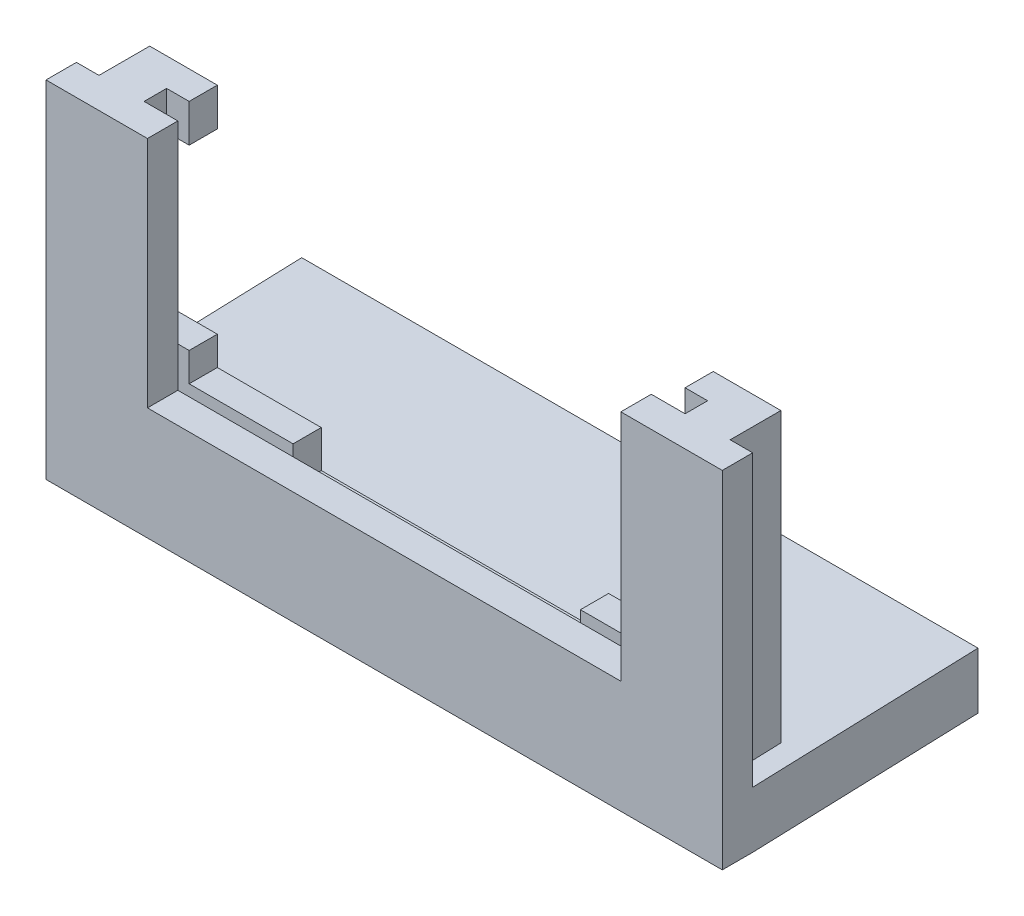
SolidWorks part; units mm, degrees
ref_plane "Front Plane" through (0, 0, 0) normal (0, 0, 1) x (1, 0, 0)
ref_plane "Top Plane" through (0, 0, 0) normal (0, 1, 0) x (1, 0, 0)
ref_plane "Right Plane" through (0, 0, 0) normal (1, 0, 0) x (0, 0, -1)
sketch "Sketch1" plane through (0, 0, 0) normal (0, 0, 1) x (1, 0, 0)
  line L0 (-33.3735, 36.8475) -> (-33.3735, -13.1525) construction
  line L1 (-63.3735, 36.8475) -> (-3.3735, 36.8475)
  line L2 (-63.3735, 36.8475) -> (-63.3735, -23.1525)
  line L3 (-63.3735, -23.1525) -> (-3.3735, -23.1525)
  line L4 (-3.3735, 36.8475) -> (-3.3735, -23.1525)
  line L5 (-54.3735, -13.1525) -> (-12.3735, -13.1525)
  line L6 (-12.3735, -13.1525) -> (-12.3735, 36.8475)
  line L7 (-54.3735, -13.1525) -> (-54.3735, 36.8475)
  dimension "D1" = 60
  dimension "D2" = 60
  dimension "D3" = 21
  dimension "D4" = 50
extrude "Boss-Extrude1" add sketch "Sketch1" along normal blind 2.7 contours L5 L7 L1 L2 L3 L4 L6
sketch "Sketch3" plane through (0, 0, 0) normal (0, 0, -1) x (-1, 0, 0)
  line L0 (54.3735, -13.1525) -> (54.3735, 36.8475) construction
  line L1 (54.3735, -13.1525) -> (12.3735, -13.1525) construction
  line L2 (12.3735, -13.1525) -> (12.3735, 36.8475) construction
  line L3 (54.3735, -13.1525) -> (54.3735, 36.8475) construction
  line L4 (54.3735, -13.1525) -> (12.3735, -13.1525) construction
  line L5 (12.3735, -13.1525) -> (12.3735, 36.8475) construction
  line L6 (9.3735, -16.1525) -> (9.3735, 36.8475)
  line L7 (57.3735, -16.1525) -> (9.3735, -16.1525)
  line L8 (57.3735, -16.1525) -> (57.3735, 36.8475)
  line L9 (61.3735, -20.1525) -> (61.3735, 36.8475)
  line L10 (61.3735, -20.1525) -> (5.3735, -20.1525)
  line L11 (5.3735, -20.1525) -> (5.3735, 36.8475)
  line L12 (5.3735, 36.8475) -> (9.3735, 36.8475)
  line L13 (57.3735, 36.8475) -> (61.3735, 36.8475)
  dimension "D1" = 3
  dimension "D2" = 4
extrude "Boss-Extrude2" add sketch "Sketch3" along normal blind 2
sketch "Sketch4" plane through (0, 0, -2) normal (0, 0, -1) x (-1, 0, 0)
  line L3 (5.3735, 36.8475) -> (5.3735, -20.1525) construction
  line L4 (5.3735, -20.1525) -> (61.3735, -20.1525) construction
  line L5 (61.3735, -20.1525) -> (61.3735, 36.8475) construction
  line L6 (55.3735, 36.8475) -> (55.3735, -14.1525)
  line L7 (55.3735, -14.1525) -> (11.3735, -14.1525)
  line L8 (11.3735, -14.1525) -> (11.3735, 36.8475)
  line L9 (55.3735, 36.8475) -> (55.3735, -14.1525)
  line L10 (55.3735, -14.1525) -> (11.3735, -14.1525)
  line L11 (11.3735, -14.1525) -> (11.3735, 36.8475)
  line L12 (5.3735, 36.8475) -> (5.3735, -20.1525)
  line L13 (5.3735, -20.1525) -> (61.3735, -20.1525)
  line L14 (61.3735, -20.1525) -> (61.3735, 36.8475)
  line L15 (11.3735, 36.8475) -> (5.3735, 36.8475)
  line L16 (55.3735, 36.8475) -> (61.3735, 36.8475)
  dimension "D1" = 2
extrude "Boss-Extrude3" add sketch "Sketch4" along normal blind 2.5
sketch "Sketch6" plane through (0, 0, 0) normal (0, 0, -1) x (-1, 0, 0)
  line L0 (63.3735, 36.8475) -> (63.3735, -23.1525) construction
  line L1 (3.3735, -23.1525) -> (63.3735, -23.1525)
  line L2 (3.3735, -23.1525) -> (3.3735, -18.1525)
  line L3 (3.3735, -18.1525) -> (63.3735, -18.1525)
  line L4 (63.3735, -23.1525) -> (63.3735, -18.1525)
  dimension "D1" = 5
extrude "Cut-Extrude5" [suppressed] cut sketch "Sketch6" against normal blind 0.4
sketch "Sketch7" [suppressed] plane through (-3.3735, 0, 0) normal (1, 0, 0) x (0, 0, -1)
  line L0 (-0.4, -19.2771) -> (38.2138, -8.9306) construction
sketch "Sketch9" plane through (0, 0, 0) normal (0, 0, -1) x (-1, 0, 0)
  line L0 (63.3735, 36.8475) -> (63.3735, -23.1525) construction
  line L1 (3.3735, -23.1525) -> (63.3735, -23.1525)
  line L2 (3.3735, -23.1525) -> (3.3735, -18.1525)
  line L3 (3.3735, -18.1525) -> (63.3735, -18.1525)
  line L4 (63.3735, -23.1525) -> (63.3735, -18.1525)
  dimension "D1" = 5
sketch3d "3DSketch1"
  line L0 (-33.3735, -20.6525, 0) -> (-33.3735, -19.9545, -19.9878)
  line L1 (-33.3735, -18.1525, 0) -> (-33.3735, -20.6525, 0) construction
  line L2 (-3.3735, -18.1525, 0) -> (-63.3735, -18.1525, 0) construction
  line L3 (-33.3735, -20.6525, 0) -> (-3.3735, -20.6525, 0) construction
  line L4 (-3.3735, -23.1525, 0) -> (-3.3735, -18.1525, 0) construction
  dimension "D1" = 88
  dimension "D2" = 20
sweep "Sweep1" add profiles "Sketch9" path "3DSketch1"
sketch "Sketch10" plane through (0, 0, -4.5) normal (0, 0, -1) x (-1, 0, 0)
  line L0 (63.3735, 36.8475) -> (63.3735, -18.1525) construction
  line L3 (3.3735, 7.5455) -> (63.3735, 7.5455)
  line L5 (3.3735, 7.5455) -> (-7.104, 7.5455)
  line L6 (-7.104, 7.5455) -> (-7.104, 46.2391)
  line L7 (-7.104, 46.2391) -> (73.5351, 46.2391)
  line L8 (73.5351, 46.2391) -> (73.5351, 7.5455)
  line L9 (73.5351, 7.5455) -> (63.3735, 7.5455)
extrude "Cut-Extrude6" cut sketch "Sketch10" against normal blind 10
sketch "Sketch11" plane through (0, 0, -4.5) normal (0, 0, -1) x (-1, 0, 0)
  line L0 (55.3735, -14.1525) -> (11.3735, -14.1525) construction
  line L1 (20.6588, -14.1525) -> (46.1517, -14.1525)
  line L2 (20.6588, -14.1525) -> (20.6588, -17.4545)
  line L3 (20.6588, -17.4545) -> (46.1517, -17.4545)
  line L4 (46.1517, -14.1525) -> (46.1517, -17.4545)
  line L5 (63.3735, -17.4545) -> (3.3735, -17.4545) construction
  line L6 (11.3735, -14.1525) -> (11.3735, 7.5455) construction
  line L7 (11.3735, 4.1801) -> (7.7534, 4.1801)
  line L8 (11.3735, 4.1801) -> (11.3735, -11.6679)
  line L9 (11.3735, -11.6679) -> (7.7534, -11.6679)
  line L10 (7.7534, 4.1801) -> (7.7534, -11.6679)
  line L11 (55.3735, 7.5455) -> (55.3735, -14.1525) construction
  line L12 (55.3735, 4.1801) -> (59.1843, 4.1801)
  line L13 (55.3735, 4.1801) -> (55.3735, -11.5897)
  line L14 (55.3735, -11.5897) -> (59.1843, -11.5897)
  line L15 (59.1843, 4.1801) -> (59.1843, -11.5897)
extrude "Cut-Extrude7" cut sketch "Sketch11" against normal up to surface (4.5 mm away) up to face at (-33.3735, -3.5535, 0)
